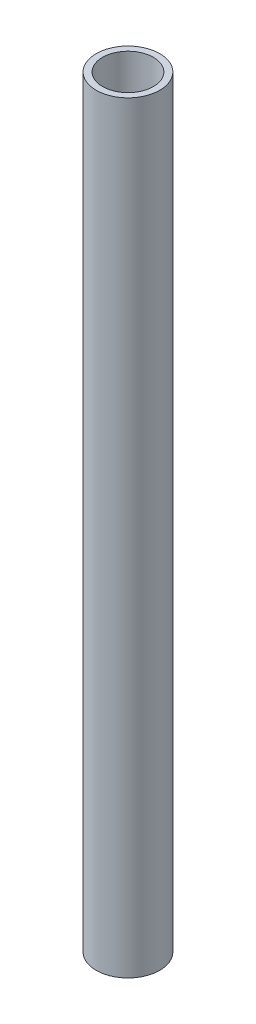
SolidWorks part; units mm, degrees
ref_plane "Front Plane" through (0, 0, 0) normal (0, 0, 1) x (1, 0, 0)
ref_plane "Top Plane" through (0, 0, 0) normal (0, 1, 0) x (1, 0, 0)
ref_plane "Right Plane" through (0, 0, 0) normal (1, 0, 0) x (0, 0, -1)
sketch "Sketch2" plane through (0, 0, 0) normal (0, 1, 0) x (1, 0, 0)
  circle A0 centre (0, 0) radius 8
  circle A1 centre (0, 0) radius 10
extrude "Boss-Extrude1" add sketch "Sketch2" along normal blind 240
